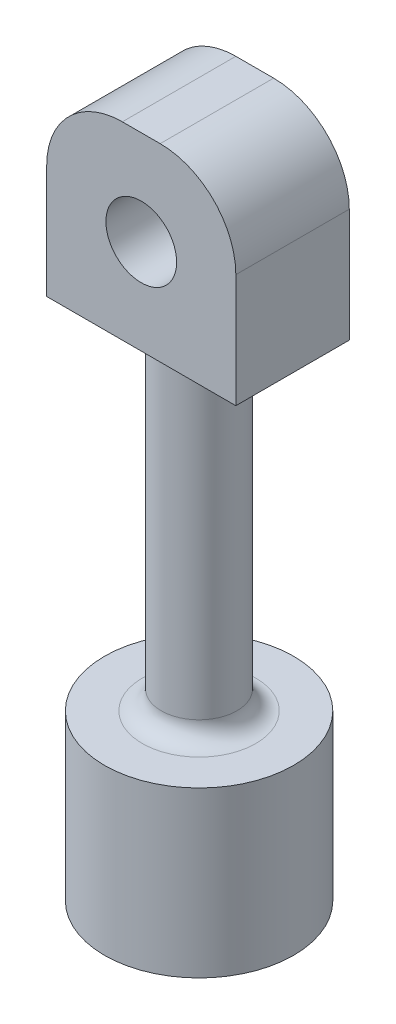
SolidWorks part; units mm, degrees
ref_plane "Front Plane" through (0, 0, 0) normal (0, 0, 1) x (1, 0, 0)
ref_plane "Top Plane" through (0, 0, 0) normal (0, 1, 0) x (1, 0, 0)
ref_plane "Right Plane" through (0, 0, 0) normal (1, 0, 0) x (0, 0, -1)
sketch "Sketch1" plane through (0, 0, 0) normal (0, 0, 1) x (1, 0, 0)
  line L1 (-2.5, 2.5) -> (2.5, 2.5)
  line L2 (-2.5, 2.5) -> (-2.5, -2.5)
  line L3 (-2.5, -2.5) -> (2.5, -2.5)
  line L4 (2.5, 2.5) -> (2.5, -2.5)
  line L5 (-2.5, 2.5) -> (2.5, -2.5) construction
  line L6 (-2.5, -2.5) -> (2.5, 2.5) construction
  circle A0 centre (0, 0) radius 0.935
  point P0 (0, 0)
  dimension "D3" = 1.87
  dimension "D1" = 5
  dimension "D2" = 5
extrude "Boss-Extrude3" add sketch "Sketch1" along normal blind 3
fillet "Fillet3" radius 2 2 edges at (-2.5, 2.5, 1.5) (2.5, 2.5, 1.5)
sketch "Sketch3" plane through (0, -2.5, 0) normal (0, -1, 0) x (1, 0, 0)
  line L0 (0, -0.0564) -> (0, 3)
  line L1 (-2.5, 3) -> (2.5, 3) construction
  circle A0 centre (0, 1.4718) radius 1
  point P5 (0, 1.4718)
extrude "Boss-Extrude4" add sketch "Sketch3" along normal blind 9 contours L0 A0 | L0 A0
fillet "Fillet5" radius 0.5 1 edges at (0, -2.5, 0.4718)
sketch "Sketch6" plane through (0, -11.5, 0) normal (0, -1, 0) x (1, 0, 0)
  circle A0 centre (0, 1.4718) radius 2.5
extrude "Boss-Extrude5" add sketch "Sketch6" along normal blind 4.35
fillet "Fillet6" radius 0.5 1 edges at (0, -11.5, 0.4718)
